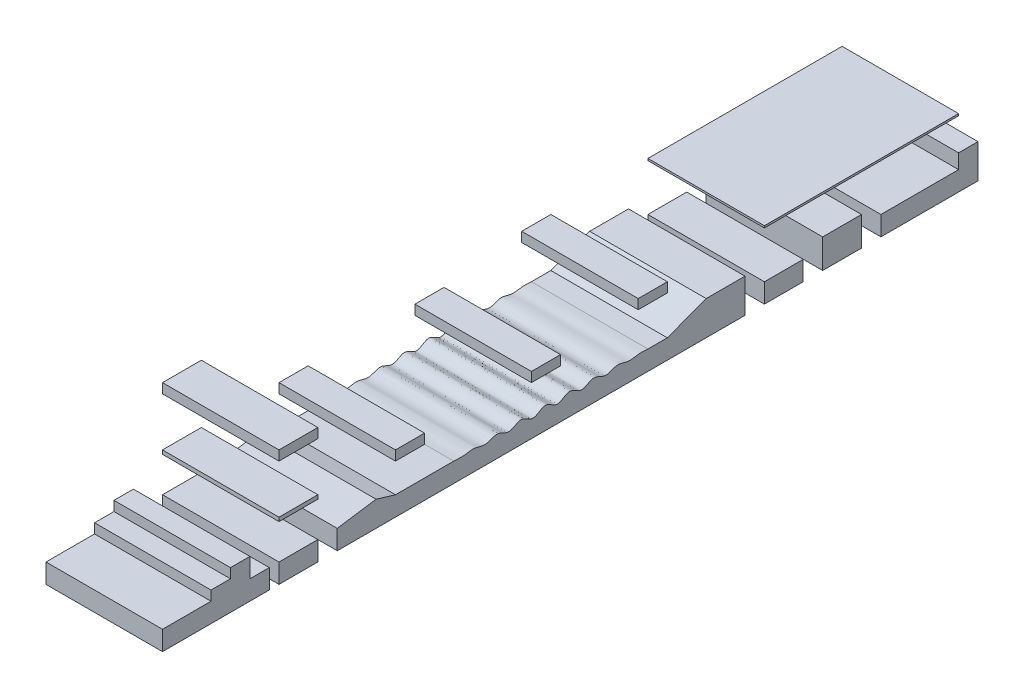
SolidWorks part; units mm, degrees
ref_plane "前视基准面" through (0, 0, 0) normal (0, 0, 1) x (1, 0, 0)
ref_plane "上视基准面" through (0, 0, 0) normal (0, 1, 0) x (1, 0, 0)
ref_plane "右视基准面" through (0, 0, 0) normal (1, 0, 0) x (0, 0, -1)
sketch "草图1" plane through (0, 0, 0) normal (1, 0, 0) x (0, 0, -1)
  line L0 (37, 0) -> (41, 0)
  line L1 (41, 0) -> (41, 0.75)
  line L2 (41, 0.75) -> (42, 0.75)
  line L3 (42, 0.75) -> (42, -1)
  line L4 (42, -1) -> (37, -1)
  line L5 (37, -1) -> (37, 0)
  line L6 (30, -1) -> (30, 0.75)
  line L7 (31, 2.5) -> (41, 2.5)
  line L8 (31, 2.5) -> (31, 2.4)
  line L9 (31, 2.4) -> (41, 2.4)
  line L10 (41, 2.5) -> (41, 2.4)
  line L11 (36, -1) -> (34, -1)
  line L12 (36, -1) -> (36, 0.5)
  line L13 (36, 0.5) -> (34, 0.5)
  line L14 (34, -1) -> (34, 0.5)
  line L15 (33, -1) -> (31, -1)
  line L16 (33, -1) -> (33, 0)
  line L17 (33, 0) -> (31, 0)
  line L18 (31, -1) -> (31, 0)
  line L19 (30, 0.75) -> (28, 0.75)
  line L20 (28, 0.75) -> (26, 0)
  line L21 (26, 0) -> (25, 0)
  line L22 (25, 0) -> (25, -1)
  line L23 (25, -1) -> (30, -1)
  line L25 (15, -1) -> (0, -1)
  line L26 (15, -1) -> (15, 0)
  line L27 (15, 0) -> (0, 0)
  line L28 (0, -1) -> (0, 0)
  point P22 (25, -0.5)
  dimension "D1" = 0.75
  dimension "D2" = 1
  dimension "D3" = 1
  dimension "D4" = 5
  dimension "D5" = 15
  dimension "D6" = 0.1
  dimension "D7" = 10
  dimension "D8" = 0
  dimension "D9" = 2.5
  dimension "D10" = 2
  dimension "D11" = 1
  dimension "D12" = 1
  dimension "D13" = 2
  dimension "D14" = 1
  dimension "D15" = 0.75
  dimension "D16" = 2
  dimension "D17" = 1
  dimension "D18" = 5
  dimension "D19" = 1
  dimension "D20" = 10
  dimension "D21" = 1.5
extrude "凸台-拉伸1" add sketch "草图1" along normal mid plane 6
sketch "草图2" plane through (0, 0, 0) normal (1, 0, 0) x (0, 0, -1)
  line L0 (25, 0) -> (25, -1)
  line L1 (25, -1) -> (15, -1)
  line L2 (15, -1) -> (15, 0)
  spline S0 degree 4 poles (13.9999, 0.053) (14.0635, 0.0537) (14.1869, 0.0408) (14.3433, -0.0015) (14.5257, -0.0222) (14.6913, -0.0175) (14.7994, -0.0073) (14.9527, 0.0002) (15.0234, 0.0007) (15.171, -0.005) (15.3045, -0.017) (15.4743, -0.0215) (15.6887, 0.0049) (15.8939, 0.0519) (16.095, 0.0449) (16.2958, -0.0092) (16.4725, -0.0666) (16.6922, -0.0797) (16.8883, 0.0005) (17.0578, 0.0713) (17.22, 0.0944) (17.3473, 0.072) (17.4652, 0.0244) (17.5781, -0.0319) (17.6985, -0.0848) (17.8355, -0.1135) (17.9705, -0.0867) (18.0885, -0.0298) (18.1953, 0.0299) (18.2964, 0.0813) (18.4194, 0.121) (18.5654, 0.1118) (18.7072, 0.0391) (18.8498, -0.049) (19.0046, -0.1291) (19.1825, -0.1255) (19.3339, -0.041) (19.474, 0.0481) (19.6259, 0.1317) (19.8039, 0.1309) (19.9554, 0.0459) (20.0952, -0.0442) (20.2467, -0.13) (20.426, -0.1323) (20.5799, -0.0476) (20.7216, 0.0426) (20.8751, 0.1269) (21.0529, 0.1268) (21.2057, 0.0471) (21.3466, -0.0394) (21.4853, -0.1096) (21.6263, -0.1201) (21.7449, -0.0852) (21.8411, -0.0386) (21.9457, 0.0191) (22.0615, 0.0777) (22.2281, 0.1207) (22.3995, 0.0714) (22.5426, -0.0047) (22.6876, -0.0648) (22.8094, -0.0908) (22.9335, -0.0812) (23.0505, -0.0458) (23.1609, -0.002) (23.2703, 0.0379) (23.4073, 0.0699) (23.5987, 0.0655) (23.8208, -0.018) (24.0772, -0.0627) (24.3234, -0.0125) (24.5349, 0.0166) (24.7014, 0.0171) (24.8329, 0.0065) (24.9777, -0.0003) (25.0477, -0.001) (25.2013, 0.0049) (25.3082, 0.0165) (25.4426, 0.024) (25.5646, 0.0193) (25.6912, 0.0002) (25.813, -0.0277) (25.9061, -0.0462) (25.9686, -0.0531) (26, -0.0553) knots 0 0 0 0 0 0.020105 0.04021 0.050263 0.060315 0.070368 0.08042 0.087985 0.09555 0.11068 0.125809 0.140939 0.165176 0.177294 0.189412 0.207123 0.224834 0.245521 0.255864 0.266208 0.276283 0.286358 0.296432 0.306507 0.318374 0.330241 0.339312 0.348383 0.357453 0.366524 0.380144 0.393763 0.407383 0.421002 0.434517 0.448032 0.461547 0.475062 0.488608 0.502154 0.515699 0.529245 0.542955 0.556664 0.570373 0.584083 0.597491 0.6109 0.624308 0.637717 0.646276 0.654836 0.663396 0.671956 0.684299 0.696643 0.716675 0.726692 0.736708 0.74645 0.756191 0.765932 0.775674 0.784484 0.793294 0.810915 0.835555 0.860195 0.875022 0.889849 0.904676 0.912089 0.919503 0.929565 0.939627 0.949689 0.959751 0.969814 0.979876 0.989938 1 1 1 1 1 construction
  spline S1 degree 4 poles (15, 0) (15.0199, 0) (15.0602, -0.0007) (15.171, -0.005) (15.3045, -0.017) (15.4743, -0.0215) (15.6887, 0.0049) (15.8939, 0.0519) (16.095, 0.0449) (16.2958, -0.0092) (16.4725, -0.0666) (16.6922, -0.0797) (16.8883, 0.0005) (17.0578, 0.0713) (17.22, 0.0944) (17.3473, 0.072) (17.4652, 0.0244) (17.5781, -0.0319) (17.6985, -0.0848) (17.8355, -0.1135) (17.9705, -0.0867) (18.0885, -0.0298) (18.1953, 0.0299) (18.2964, 0.0813) (18.4194, 0.121) (18.5654, 0.1118) (18.7072, 0.0391) (18.8498, -0.049) (19.0046, -0.1291) (19.1825, -0.1255) (19.3339, -0.041) (19.474, 0.0481) (19.6259, 0.1317) (19.8039, 0.1309) (19.9554, 0.0459) (20.0952, -0.0442) (20.2467, -0.13) (20.426, -0.1323) (20.5799, -0.0476) (20.7216, 0.0426) (20.8751, 0.1269) (21.0529, 0.1268) (21.2057, 0.0471) (21.3466, -0.0394) (21.4853, -0.1096) (21.6263, -0.1201) (21.7449, -0.0852) (21.8411, -0.0386) (21.9457, 0.0191) (22.0615, 0.0777) (22.2281, 0.1207) (22.3995, 0.0714) (22.5426, -0.0047) (22.6876, -0.0648) (22.8094, -0.0908) (22.9335, -0.0812) (23.0505, -0.0458) (23.1609, -0.002) (23.2703, 0.0379) (23.4073, 0.0699) (23.5987, 0.0655) (23.8208, -0.018) (24.0772, -0.0627) (24.3234, -0.0125) (24.5349, 0.0166) (24.7014, 0.0171) (24.8329, 0.0065) (24.941, 0.0014) (24.9805, 0.0003) (25, 0) knots 0.08042 0.08042 0.08042 0.08042 0.08042 0.087985 0.09555 0.11068 0.125809 0.140939 0.165176 0.177294 0.189412 0.207123 0.224834 0.245521 0.255864 0.266208 0.276283 0.286358 0.296432 0.306507 0.318374 0.330241 0.339312 0.348383 0.357453 0.366524 0.380144 0.393763 0.407383 0.421002 0.434517 0.448032 0.461547 0.475062 0.488608 0.502154 0.515699 0.529245 0.542955 0.556664 0.570373 0.584083 0.597491 0.6109 0.624308 0.637717 0.646276 0.654836 0.663396 0.671956 0.684299 0.696643 0.716675 0.726692 0.736708 0.74645 0.756191 0.765932 0.775674 0.784484 0.793294 0.810915 0.835555 0.860195 0.875022 0.889849 0.904676 0.912089 0.919503 0.919503 0.919503 0.919503 0.919503
  point P8 (3.7114, 5.671)
extrude "凸台-拉伸2" add sketch "草图2" along direction (1, 0, 0) on the side of the normal up to surface (3 mm away) and the other way up to surface (3 mm away)
sketch "草图3" plane through (0, 0, 0) normal (1, 0, 0) x (0, 0, -1)
  line L0 (2.5, 0) -> (2.5, 0.5)
  line L1 (15, 0) -> (0, 0) construction
  line L2 (2.5, 0.5) -> (3.5, 0.5)
  line L3 (3.5, 0.5) -> (3.5, 1)
  line L4 (3.5, 1) -> (4.5, 1)
  line L5 (4.5, 1) -> (4.5, 0)
  line L6 (4.5, 0) -> (2.5, 0)
  dimension "D1" = 0.5
  dimension "D2" = 0.5
  dimension "D3" = 1
  dimension "D4" = 1
  dimension "D5" = 2.5
extrude "凸台-拉伸3" add sketch "草图3" along direction (-1, 0, 0) on the side of the normal up to surface (3 mm away) and the other way up to surface (3 mm away)
sketch "草图4" plane through (0, 0, 0) normal (1, 0, 0) x (0, 0, -1)
  line L0 (15, 0) -> (4.5, 0) construction
  line L1 (5.5, 0) -> (6, 0)
  line L2 (5.5, 0) -> (5.5, -1)
  line L3 (5.5, -1) -> (6, -1)
  line L4 (6, 0) -> (6, -1)
  line L5 (0, -1) -> (30, -1) construction
  line L6 (4.5, 0) -> (4.5, 1) construction
  line L8 (8, 0) -> (9, 0)
  line L9 (8, 0) -> (8, -1)
  line L10 (8, -1) -> (9, -1)
  line L11 (9, 0) -> (9, -1)
  dimension "D1" = 0.5
  dimension "D2" = 1
  dimension "D3" = 2
  dimension "D4" = 1
extrude "切除-拉伸1" cut sketch "草图4" against normal through all from surface at 3 starting at face at (3, 0.1786, -12.8571)
sketch "草图5" plane through (0, 0, 0) normal (1, 0, 0) x (0, 0, -1)
  line L0 (4.5, 1) -> (3.5, 1) construction
  line L1 (6, 1.8) -> (8, 1.8)
  line L2 (6, 1.8) -> (6, 2)
  line L3 (6, 2) -> (8, 2)
  line L4 (8, 1.8) -> (8, 2)
  line L5 (6, 0) -> (6, -1) construction
  line L6 (8, -1) -> (8, 0) construction
  dimension "D1" = 1
  dimension "D2" = 0.2
extrude "凸台-拉伸4" add sketch "草图5" along normal up to surface and the other way up to surface separate body up to face at (3, 0.1, -3.2) other way up to face at (-3, -0.0625, -20.875)
sketch "草图6" plane through (0, 0, 0) normal (1, 0, 0) x (0, 0, -1)
  line L0 (9, 0) -> (11, 0.3)
  line L1 (11, 0.3) -> (12, 0)
  line L2 (15, 0) -> (9, 0) construction
  line L3 (12, 0) -> (9, 0)
  dimension "D1" = 3
  dimension "D2" = 0.3
  dimension "D3" = 2
extrude "凸台-拉伸5" add sketch "草图6" along normal up to surface and the other way up to surface contours L3 L0 L1 up to face at (3, -0.0625, -22.125) other way up to face at (-3, -0.0625, -20.875)
sketch "草图7" plane through (0, 0, 0) normal (1, 0, 0) x (0, 0, -1)
  line L0 (15, 0) -> (12, 0) construction
  line L1 (12, 2) -> (13.5, 2)
  line L2 (12, 2) -> (12, 1.5)
  line L3 (12, 1.5) -> (13.5, 1.5)
  line L4 (13.5, 2) -> (13.5, 1.5)
  line L5 (9, 0) -> (9, -1) construction
  line L6 (24.5, 2) -> (26, 2)
  line L7 (24.5, 2) -> (24.5, 2.5)
  line L8 (24.5, 2.5) -> (26, 2.5)
  line L9 (26, 2) -> (26, 2.5)
  line L10 (26, 0) -> (25, 0) construction
  line L11 (20.5, 1.5) -> (19, 1.5)
  line L12 (20.5, 1.5) -> (20.5, 2)
  line L13 (20.5, 2) -> (19, 2)
  line L14 (19, 1.5) -> (19, 2)
  line L15 (8, 2) -> (6, 2) construction
  line L16 (6, 5) -> (8, 5)
  line L17 (6, 5) -> (6, 4.5)
  line L18 (6, 4.5) -> (8, 4.5)
  line L19 (8, 5) -> (8, 4.5)
  line L20 (6, 2) -> (6, 1.8) construction
  dimension "D1" = 1.5
  dimension "D2" = 0.5
  dimension "D3" = 1.5
  dimension "D4" = 1.5
  dimension "D5" = 0.5
  dimension "D6" = 0
  dimension "D7" = 2
  dimension "D8" = 3
  dimension "D9" = 0.5
  dimension "D10" = 1.5
  dimension "D11" = 1.5
  dimension "D12" = 4
  dimension "D13" = 2
  dimension "D14" = 2.5
  dimension "D15" = 0.5
  dimension "D16" = 0
extrude "凸台-拉伸6" add sketch "草图7" along normal up to surface and the other way up to surface separate body
